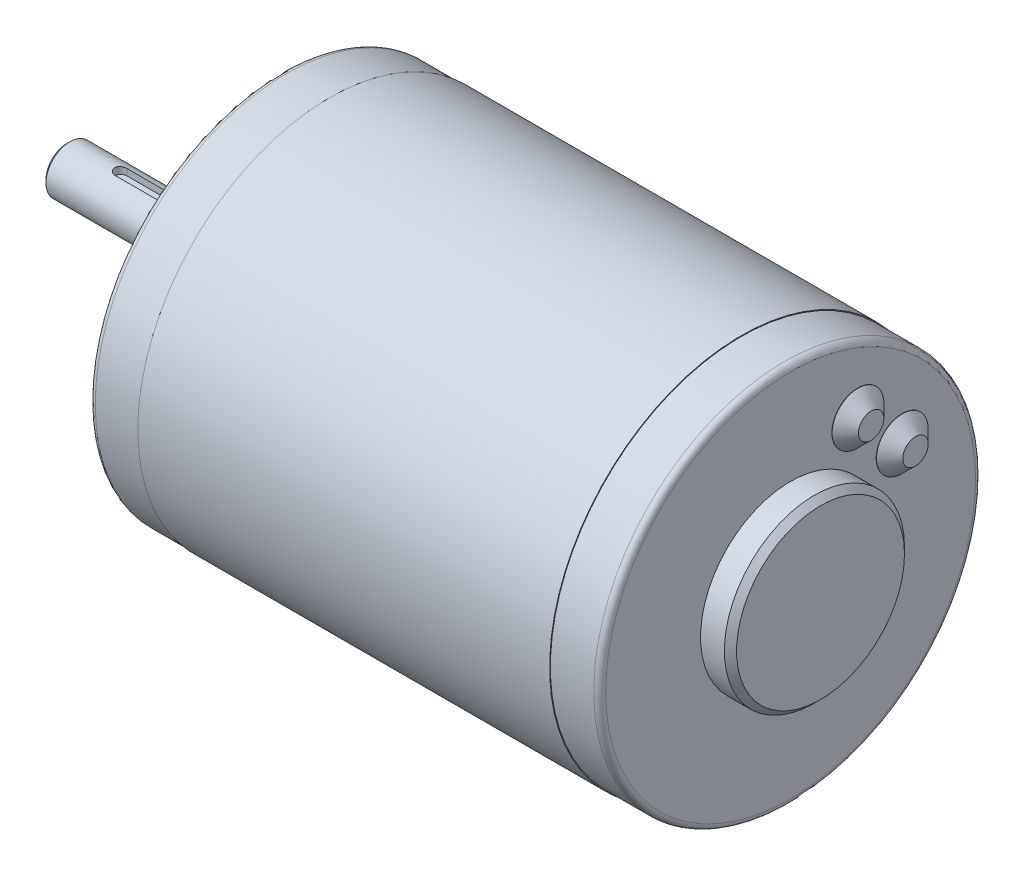
SolidWorks part; units mm, degrees
ref_plane "Front Plane" through (0, 0, 0) normal (0, 0, 1) x (1, 0, 0)
ref_plane "Top Plane" through (0, 0, 0) normal (0, 1, 0) x (1, 0, 0)
ref_plane "Right Plane" through (0, 0, 0) normal (1, 0, 0) x (0, 0, -1)
sketch "Sketch1" plane through (0, 0, 0) normal (0, 0, 1) x (1, 0, 0)
  line L0 (8.2296, 32.004) -> (8.2296, 0)
  line L1 (8.2296, 0) -> (76.9864, 0)
  line L2 (76.9864, 0) -> (76.9864, 32.004)
  line L3 (76.9864, 32.004) -> (8.2296, 32.004)
  line L4 (8.2296, 0) -> (76.9864, 0) construction
revolve "Revolve1" add sketch "Sketch1" angle 360 about L4
sketch "Sketch2" plane through (76.9864, 0, 0) normal (1, 0, 0) x (0, 0, -1)
  circle A0 centre (0, 0) radius 31.877
extrude "Boss-Extrude1" add sketch "Sketch2" along normal blind 8.2296
sketch "Sketch3" plane through (85.216, 0, 0) normal (1, 0, 0) x (0, 0, -1)
  circle A0 centre (0, 0) radius 15.0368
extrude "Boss-Extrude2" add sketch "Sketch3" along normal blind 5
sketch "Sketch4" plane through (8.2296, 0, 0) normal (-1, 0, 0) x (0, 0, 1)
  circle A0 centre (0, 0) radius 31.877
extrude "Boss-Extrude3" add sketch "Sketch4" along normal blind 8.2296
sketch "Sketch5" plane through (0, 0, 0) normal (-1, 0, 0) x (0, 0, 1)
  circle A0 centre (0, 0) radius 9.525
extrude "Boss-Extrude4" add sketch "Sketch5" along normal blind 4
sketch "Sketch6" plane through (-4, 0, 0) normal (-1, 0, 0) x (0, 0, 1)
  circle A0 centre (0, 0) radius 4
extrude "Boss-Extrude5" add sketch "Sketch6" along normal blind 31.6
imported_body "Surface-Imported1"
ref_plane "Plane1" through (0, 2.8, 0) normal (0, -1, 0) x (1, 0, 0)
sketch "Sketch7" plane through (0, 2.8, 0) normal (0, -1, 0) x (1, 0, 0)
  line L0 (-7.1, 1) -> (-26.6, 1)
  line L1 (-26.6, -1) -> (-7.1, -1)
  arc A0 (-7.1, -1) -> (-7.1, 1) centre (-7.1, 0) ccw
  arc A1 (-26.6, 1) -> (-26.6, -1) centre (-26.6, 0) ccw
extrude "Cut-Extrude1" cut sketch "Sketch7" against normal up to surface
ref_plane "Plane2" through (0, 0, -18.6071) normal (0, 0, 1) x (1, 0, 0)
sketch "Sketch8" plane through (0, 0, -18.6071) normal (0, 0, 1) x (1, 0, 0)
  line L0 (85.216, 15.5254) -> (85.216, 11.2074)
  line L1 (85.216, 11.2074) -> (87.4639, 11.2074)
  line L2 (87.4639, 11.2074) -> (87.4639, 13.3254)
  line L3 (87.4639, 13.3254) -> (85.2639, 15.5254)
  line L4 (85.2639, 15.5254) -> (85.216, 15.5254)
  line L5 (85.216, 11.2074) -> (87.4639, 11.2074) construction
revolve "Revolve2" add sketch "Sketch8" angle 360 about L5
ref_plane "Plane3" through (0, 0, -11.2074) normal (0, 0, 1) x (1, 0, 0)
sketch "Sketch9" plane through (0, 0, -11.2074) normal (0, 0, 1) x (1, 0, 0)
  line L0 (85.216, 22.9251) -> (85.216, 18.6071)
  line L1 (85.216, 18.6071) -> (87.4639, 18.6071)
  line L2 (87.4639, 18.6071) -> (87.4639, 20.7251)
  line L3 (87.4639, 20.7251) -> (85.2639, 22.9251)
  line L4 (85.2639, 22.9251) -> (85.216, 22.9251)
  line L5 (85.216, 18.6071) -> (87.4639, 18.6071) construction
revolve "Revolve3" add sketch "Sketch9" angle 360 about L5
hole_wizard "M3.5 Clearance Hole1" positions "Sketch11" profile "Sketch10" hole size "M3.5" standard "ANSI Metric"
sketch "Sketch11" plane through (0, 0, 0) normal (-1, 0, 0) x (0, 0, 1)
  point P0 (0, 25.4)
  point P1 (0, -25.4)
sketch "Sketch10" plane through (0, 25.4, 0) normal (0, 1, 0) x (0, 0, 1)
  line L0 (0, 0) -> (0, 14.8277)
  line L1 (0, 14.8277) -> (2.0193, 13.6144)
  line L2 (2.0193, 13.6144) -> (2.0193, 0)
  line L5 (2.0193, 0) -> (0, 0)
  line L10 (0, 14.8277) -> (-2.0193, 13.6144) construction
  line L11 (0, -6.35) -> (0, 107.95) construction
  dimension "Hole Dia." = 4.0386
  dimension "Hole Depth" = 13.6144
  dimension "Drill Angle" = 118
chamfer "Chamfer1" distance 1.016 angle 45 2 edges at (-4, 0, 9.525) (90.216, 0, -15.0368)
chamfer "Chamfer2" distance 0.5 angle 45 1 edges at (-35.6, 0, 4)
fillet "Fillet1" radius 1 2 edges at (0, 0, 31.877) (85.216, 0, -31.877)
